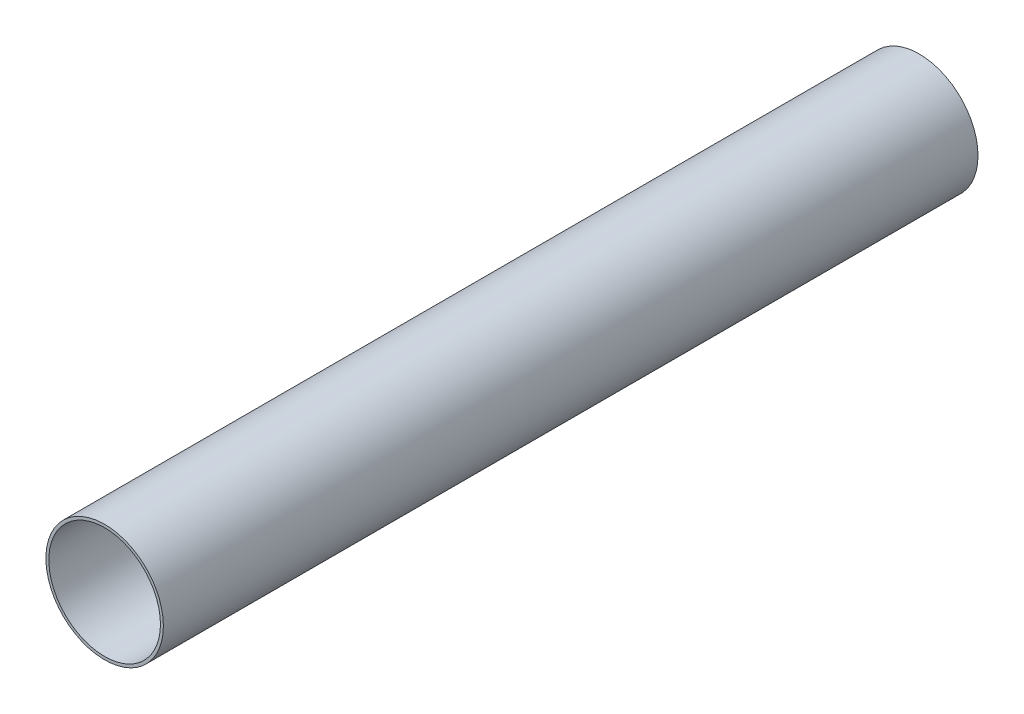
SolidWorks part; units mm, degrees
ref_plane "Front Plane" through (0, 0, 0) normal (0, 0, 1) x (1, 0, 0)
ref_plane "Top Plane" through (0, 0, 0) normal (0, 1, 0) x (1, 0, 0)
ref_plane "Right Plane" through (0, 0, 0) normal (1, 0, 0) x (0, 0, -1)
sketch "Sketch1" plane through (0, 0, 0) normal (0, 0, 1) x (1, 0, 0)
  circle A0 centre (0, 0) radius 15.265
  circle A1 centre (0, 0) radius 14.505
  dimension "D1" = 0.76
extrude "Boss-Extrude1" add sketch "Sketch1" along normal blind 211.7
